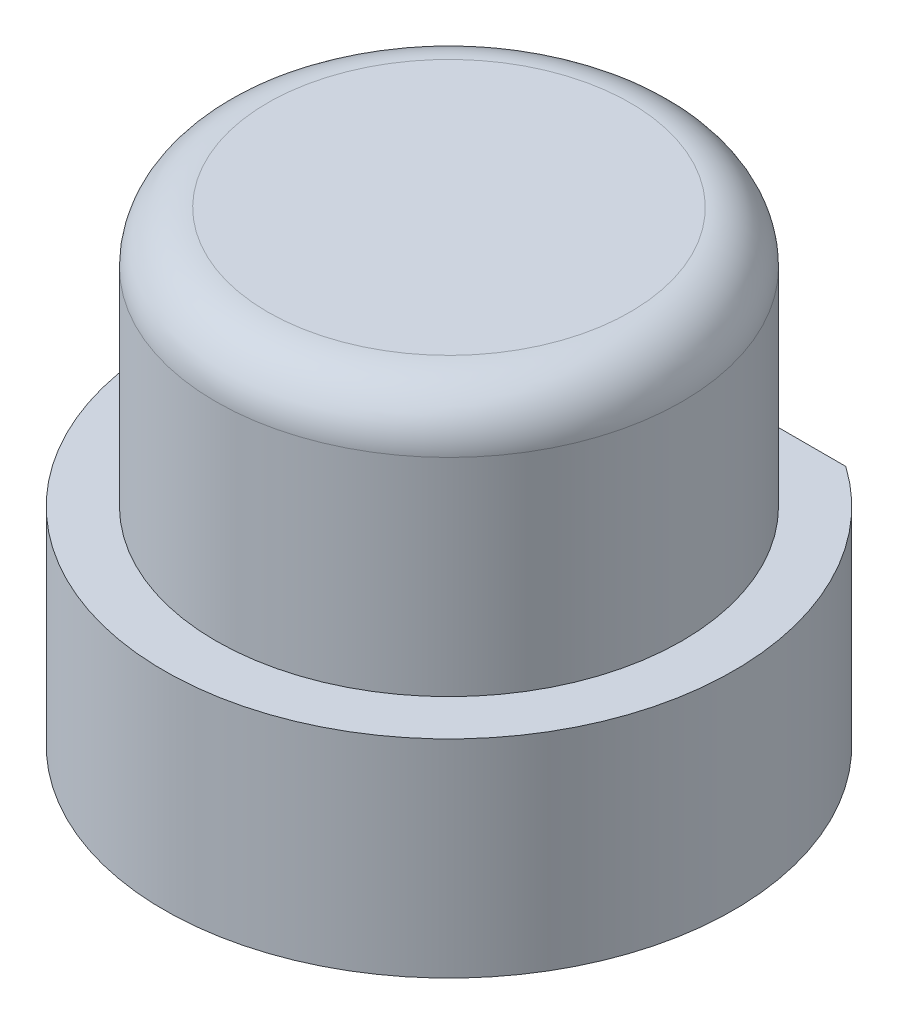
SolidWorks part; units mm, degrees
ref_plane "Ön Düzlem" through (0, 0, 0) normal (0, 0, 1) x (1, 0, 0)
ref_plane "Üst Düzlem" through (0, 0, 0) normal (0, 1, 0) x (1, 0, 0)
ref_plane "Sağ Düzlem" through (0, 0, 0) normal (1, 0, 0) x (0, 0, -1)
sketch "Çizim1" plane through (0, 0, 0) normal (0, 1, 0) x (1, 0, 0)
  line L0 (3.1623, 4.5) -> (-3.1623, 4.5)
  arc A0 (-3.1623, 4.5) -> (3.1623, 4.5) centre (0, 0) ccw
  dimension "D1" = 11
  dimension "D2" = 4.5
extrude "Yükseklik-Ekstrüzyon1" add sketch "Çizim1" along normal blind 9
sketch "Çizim2" plane through (0, 0, 0) normal (0, -1, 0) x (1, 0, 0)
  circle A0 centre (0, 0) radius 3.5
  dimension "D1" = 7
extrude "Kes-Ekstrüzyon1" cut sketch "Çizim2" against normal blind 1.5
sketch "Çizim3" plane through (0, 9, 0) normal (0, 1, 0) x (1, 0, 0)
  circle A0 centre (0, 0) radius 6
  circle A1 centre (0, 0) radius 4.5
  dimension "D1" = 9
  dimension "D2" = 12
extrude "Kes-Ekstrüzyon2" cut sketch "Çizim3" against normal blind 5
fillet "Radyus1" radius 1 1 edges at (0, 9, 4.5)
